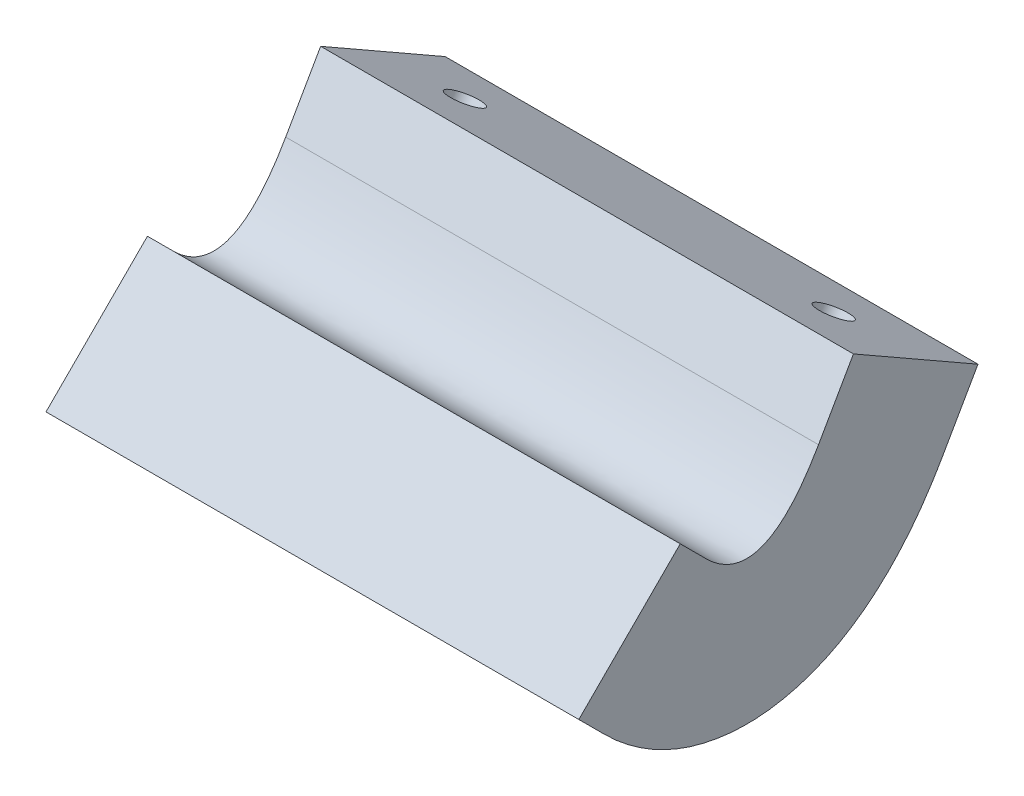
SolidWorks part; units mm, degrees
ref_plane "Front Plane" through (0, 0, 0) normal (0, 0, 1) x (1, 0, 0)
ref_plane "Top Plane" through (0, 0, 0) normal (0, 1, 0) x (1, 0, 0)
ref_plane "Right Plane" through (0, 0, 0) normal (1, 0, 0) x (0, 0, -1)
sketch "Sketch1" plane through (0, 0, 0) normal (1, 0, 0) x (0, 0, -1)
  line L0 (0, 0) -> (0, 10) construction
  line L1 (3.5, 3.0625) -> (5.2051, 6.0464)
  line L2 (-2, 1) -> (-3.2471, 2.2471)
  line L3 (-6.9497, -3.9497) -> (-8.1969, -2.7026)
  line L4 (9.5777, -0.4105) -> (11.2828, 2.5734)
  line L5 (11.2828, 2.5734) -> (5.2051, 6.0464)
  line L6 (-3.2471, 2.2471) -> (-8.1969, -2.7026)
  spline S0 degree 2 poles (-2.4771, 1.534) (0.6828, -2.3797) (3.8427, 3.6916) knots 0 0 0 1 1 1 construction
  spline S1 degree 2 poles (-2, 1) (0.75, -1.75) (3.5, 3.0625) knots 0.075491 0.075491 0.075491 0.945774 0.945774 0.945774
  spline S2 degree 1 poles (-6.9497, -3.9497) (9.5777, -0.4105) knots 0 0 1 1 construction
  spline S3 degree 3 poles (-6.9497, -3.9497) (-6.6854, -4.2141) (-6.1476, -4.7083) (-4.8591, -5.6745) (-2.827, -6.7128) (0.2959, -7.1842) (3.3303, -6.5242) (5.63, -5.2011) (7.8397, -3.1681) (8.9128, -1.574) (9.5777, -0.4105) knots 0.075491 0.075491 0.075491 0.075491 0.129884 0.184277 0.293062 0.401847 0.510633 0.619418 0.728204 0.945774 0.945774 0.945774 0.945774
  dimension "D1" = 7
extrude "Boss-Extrude1" add sketch "Sketch1" along normal blind 26
sketch "Sketch2" plane through (0, 7.6419, -2.4128) normal (0, 0.8682, -0.4961) x (1, 0, 0)
  line L0 (0, 6.716) -> (26, 6.716) construction
  line L3 (4, 6.716) -> (22, 6.716)
  line L4 (0, 10.216) -> (0, 3.216) construction
  line L5 (26, 10.216) -> (26, 3.216) construction
  point P2 (0, 6.805)
  point P5 (26, 6.805)
  point P9 (13, 6.716)
sketch "Sketch3" plane through (0, 7.6419, -2.4128) normal (0, 0.8682, -0.4961) x (1, 0, 0)
  circle A0 centre (4, 6.716) radius 0.8
  circle A1 centre (22, 6.716) radius 0.8
extrude "Cut-Extrude1" cut sketch "Sketch3" against normal blind 7
